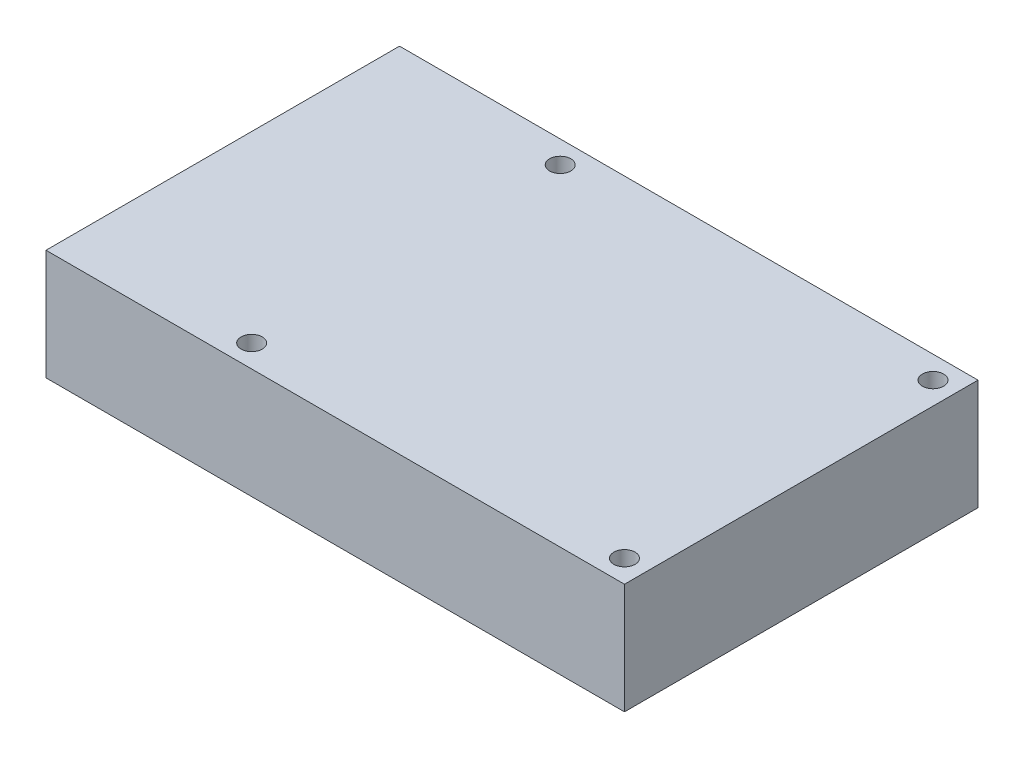
SolidWorks part; units mm, degrees
ref_plane "Front Plane" through (0, 0, 0) normal (0, 0, 1) x (1, 0, 0)
ref_plane "Top Plane" through (0, 0, 0) normal (0, 1, 0) x (1, 0, 0)
ref_plane "Right Plane" through (0, 0, 0) normal (1, 0, 0) x (0, 0, -1)
sketch "Sketch1" plane through (0, 0, 0) normal (0, 1, 0) x (1, 0, 0)
  line L1 (-45, -27.5) -> (45, -27.5)
  line L2 (-45, -27.5) -> (-45, 27.5)
  line L3 (-45, 27.5) -> (45, 27.5)
  line L4 (45, -27.5) -> (45, 27.5)
  line L5 (-45, -27.5) -> (45, 27.5) construction
  line L6 (-45, 27.5) -> (45, -27.5) construction
  point P0 (0, 0)
  dimension "D1" = 90
  dimension "D2" = 55
extrude "Boss-Extrude2" add sketch "Sketch1" along normal blind 17.2
sketch "Sketch2" plane through (0, 17.2, 0) normal (0, 1, 0) x (1, 0, 0)
  line L0 (45, 27.5) -> (-45, 27.5) construction
  line L1 (45, -27.5) -> (45, 27.5) construction
  line L2 (-45, -27.5) -> (45, -27.5) construction
  circle A0 centre (41.5, 24) radius 1.65
  circle A1 centre (41.5, -24) radius 1.65
  circle A2 centre (-16.5, -24) radius 1.65
  circle A3 centre (-16.5, 24) radius 1.65
  dimension "D3" = 3.3
  dimension "D6" = 3.3
  dimension "D9" = 3.3
  dimension "D10" = 3.3
  dimension "D1" = 3.5
  dimension "D2" = 3.5
  dimension "D4" = 3.5
  dimension "D5" = 3.5
  dimension "D7" = 58
  dimension "D8" = 3.5
  dimension "D11" = 3.5
  dimension "D12" = 58
extrude "Cut-Extrude1" cut sketch "Sketch2" against normal through all
